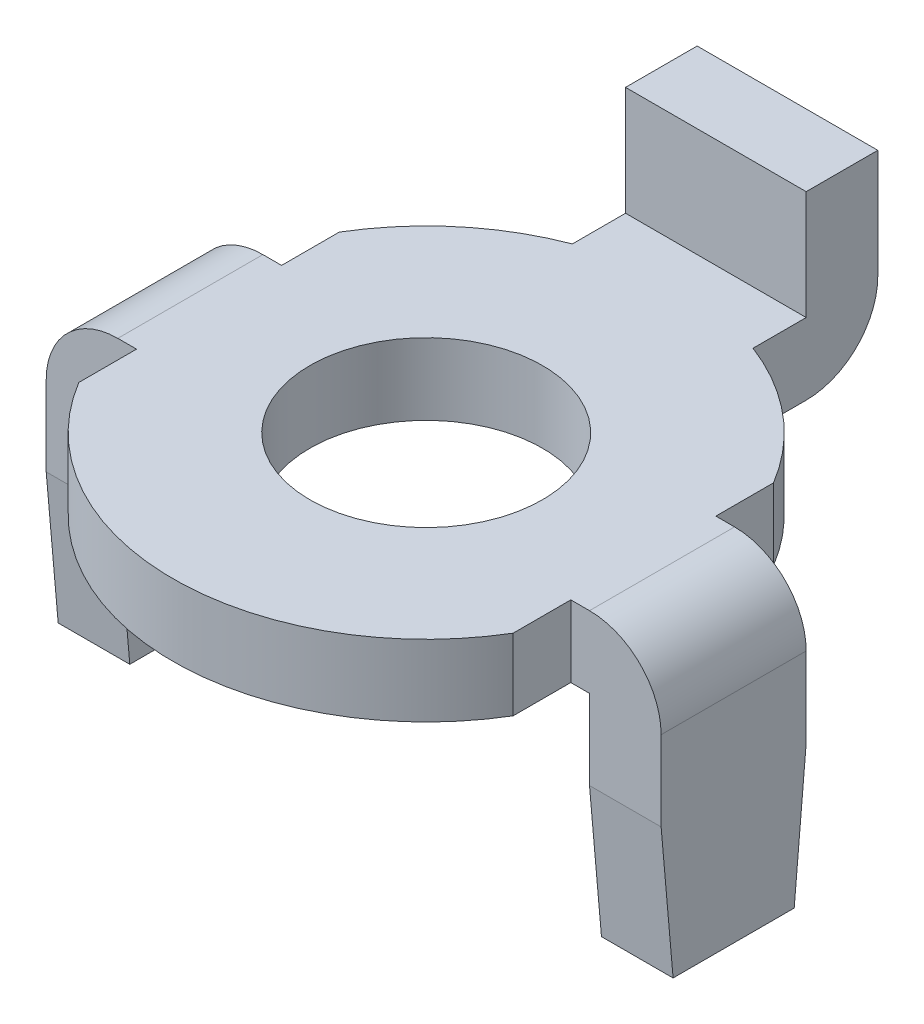
SolidWorks part; units mm, degrees
material "Nickel silver 65-12, UNS C75700"
ref_plane "Front Plane" through (0, 0, 0) normal (0, 0, 1) x (1, 0, 0)
ref_plane "Top Plane" through (0, 0, 0) normal (0, 1, 0) x (1, 0, 0)
ref_plane "Right Plane" through (0, 0, 0) normal (1, 0, 0) x (0, 0, -1)
sketch "Sketch1" plane through (0, 0, 0) normal (0, 1, 0) x (1, 0, 0)
  line L0 (-4.76, 2.8539) -> (-4.76, 1.59)
  line L1 (4.76, 2.8539) -> (4.76, 1.59)
  line L2 (0, 0) -> (-11.0316, 0) construction
  line L3 (-4.76, 1.59) -> (-6.74, 1.59)
  line L4 (-6.74, 1.59) -> (-6.74, -1.59)
  line L5 (-6.74, -1.59) -> (-4.76, -1.59)
  line L6 (-4.76, -1.59) -> (-4.76, -2.8539)
  line L7 (4.76, 1.59) -> (6.74, 1.59)
  line L8 (6.74, 1.59) -> (6.74, -1.59)
  line L9 (6.74, -1.59) -> (4.76, -1.59)
  line L10 (4.76, -1.59) -> (4.76, -2.8539)
  line L11 (-1.98, 7.92) -> (-1.98, 5.1848)
  line L12 (-1.98, 7.92) -> (1.98, 7.92)
  line L13 (1.98, 7.92) -> (1.98, 5.1848)
  arc A0 (-4.76, -2.8539) -> (4.76, -2.8539) centre (0, 0) ccw
  circle A1 centre (0, 0) radius 2.55
  arc A2 (4.76, 2.8539) -> (1.98, 5.1848) centre (0, 0) ccw
  arc A3 (-1.98, 5.1848) -> (-4.76, 2.8539) centre (0, 0) ccw
  point P10 (-6.74, 0)
  point P19 (0, 7.92)
  dimension "D1" = 11.1
  dimension "D2" = 5.1
  dimension "D3" = 9.52
  dimension "D4" = 3.18
  dimension "D5" = 4.76
  dimension "D6" = 13.48
  dimension "D7" = 3.96
  dimension "D8" = 7.92
extrude "Boss-Extrude1" add sketch "Sketch1" along normal blind 1.57
sketch "Sketch2" plane through (0, 0, 0) normal (0, -1, 0) x (1, 0, 0)
  line L0 (-4.76, -1.59) -> (-6.74, -1.59) construction
  line L1 (-6.74, 1.59) -> (-5.17, 1.59)
  line L2 (-6.74, 1.59) -> (-6.74, -1.59)
  line L3 (-6.74, -1.59) -> (-5.17, -1.59)
  line L4 (-5.17, 1.59) -> (-5.17, -1.59)
  line L5 (6.74, -1.59) -> (4.76, -1.59) construction
  line L6 (6.74, 1.59) -> (5.17, 1.59)
  line L7 (6.74, 1.59) -> (6.74, -1.59)
  line L8 (6.74, -1.59) -> (5.17, -1.59)
  line L9 (5.17, 1.59) -> (5.17, -1.59)
  dimension "D1" = 1.57
  dimension "D2" = 1.57
extrude "Boss-Extrude2" add sketch "Sketch2" along normal blind 4.75
sketch "Sketch3" plane through (0, 1.57, 0) normal (0, 1, 0) x (1, 0, 0)
  line L0 (1.98, 5.1848) -> (1.98, 7.92) construction
  line L1 (-1.98, 7.92) -> (1.98, 7.92)
  line L2 (-1.98, 7.92) -> (-1.98, 6.35)
  line L3 (-1.98, 6.35) -> (1.98, 6.35)
  line L4 (1.98, 7.92) -> (1.98, 6.35)
  dimension "D1" = 1.57
extrude "Boss-Extrude3" add sketch "Sketch3" along normal blind 2.39
fillet "Fillet1" radius 1.57 3 edges at (-6.74, 1.57, 0) (6.74, 1.57, 0) (0, 0, -7.92)
chamfer "Chamfer1" distance 3 angle 5 4 edges at (5.955, -4.75, -1.59) (5.955, -4.75, 1.59) (-5.955, -4.75, -1.59) (-5.955, -4.75, 1.59)
